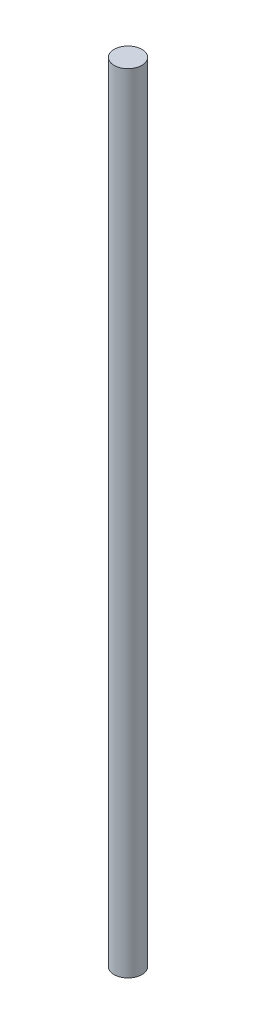
SolidWorks part; units mm, degrees
ref_plane "Alzado" through (0, 0, 0) normal (0, 0, 1) x (1, 0, 0)
ref_plane "Planta" through (0, 0, 0) normal (0, 1, 0) x (1, 0, 0)
ref_plane "Vista lateral" through (0, 0, 0) normal (1, 0, 0) x (0, 0, -1)
sketch "Croquis1" plane through (0, 0, 0) normal (0, 1, 0) x (1, 0, 0)
  circle A0 centre (0, 0) radius 6.35
  dimension "D1" = 12.7
sketch "Croquis2" plane through (0, 0, 0) normal (0, 0, 1) x (1, 0, 0)
  line L0 (0, 0) -> (0, 360)
  dimension "D1" = 360
sweep "Barrer1" add profiles "Croquis1" path "Croquis2"
